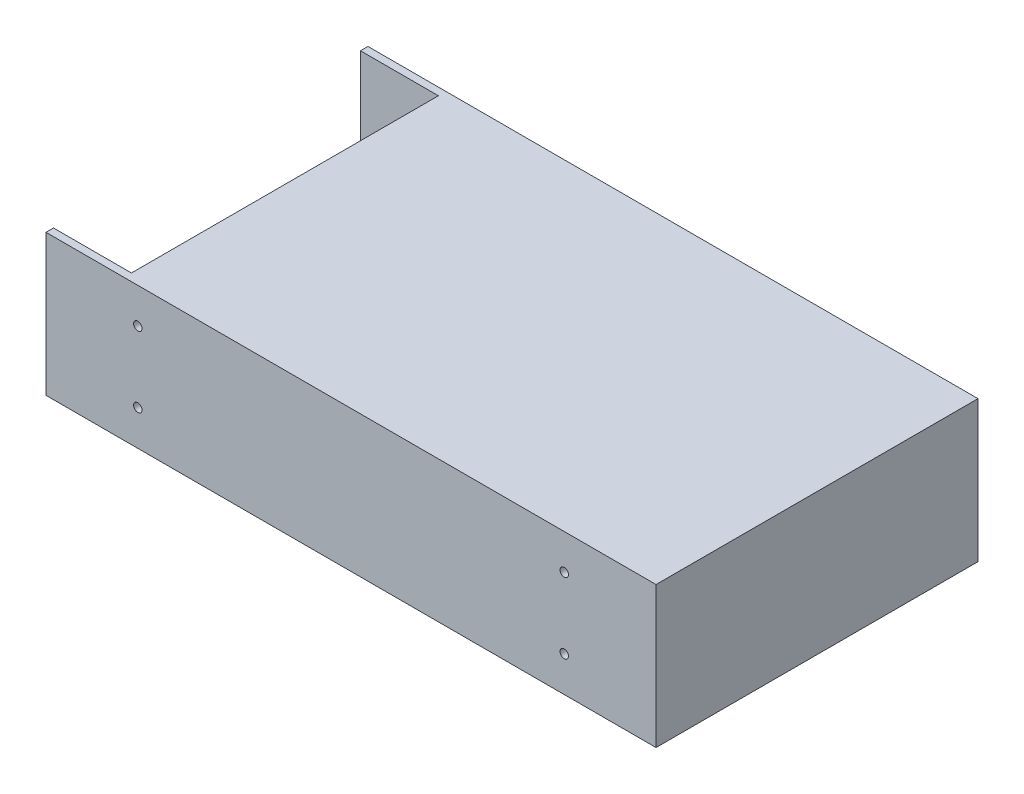
SolidWorks part; units mm, degrees
ref_plane "前视基准面" through (0, 0, 0) normal (0, 0, 1) x (1, 0, 0)
ref_plane "上视基准面" through (0, 0, 0) normal (0, 1, 0) x (1, 0, 0)
ref_plane "右视基准面" through (0, 0, 0) normal (1, 0, 0) x (0, 0, -1)
sketch "草图1" plane through (0, 0, 0) normal (0, 1, 0) x (1, 0, 0)
  line L0 (0, 0) -> (48559.8577, 0) construction
  line L1 (0, 0) -> (0, 48559.8577) construction
  line L3 (-108, 57) -> (108, 57)
  line L4 (-108, 57) -> (-108, -57)
  line L5 (-108, -57) -> (108, -57)
  line L6 (108, 57) -> (108, -57)
  dimension "D1" = 216
  dimension "D2" = 114
extrude "凸台-拉伸1" add sketch "草图1" along normal blind 50
sketch "草图2" plane through (0, 50, 0) normal (0, 1, 0) x (1, 0, 0)
  line L0 (-108, 57) -> (-108, -57) construction
  line L1 (-108, 54.3417) -> (-80.4049, 54.3417)
  line L2 (-108, 54.3417) -> (-108, -54.3417)
  line L3 (-108, -54.3417) -> (-80.4049, -54.3417)
  line L4 (-80.4049, 54.3417) -> (-80.4049, -54.3417)
extrude "切除-拉伸1" cut sketch "草图2" against normal blind 44
sketch "草图3" plane through (0, 6, 0) normal (0, 1, 0) x (1, 0, 0)
  line L1 (-102.2979, 47.8259) -> (-86.9207, 47.8259)
  line L2 (-102.2979, 47.8259) -> (-102.2979, -47.5653)
  line L3 (-102.2979, -47.5653) -> (-86.9207, -47.5653)
  line L4 (-86.9207, 47.8259) -> (-86.9207, -47.5653)
extrude "凸台-拉伸2" add sketch "草图3" along normal blind 10
sketch "草图4" plane through (0, 0, 57) normal (0, 0, 1) x (1, 0, 0)
  line L0 (108, 50) -> (108, 0) construction
  line L1 (-108, 0) -> (108, 0) construction
  circle A0 centre (75.5, 37.5) radius 1.5
  circle A1 centre (75.5, 12.5) radius 1.5
  circle A2 centre (-75.5, 12.5) radius 1.5
  circle A3 centre (-75.5, 37.5) radius 1.5
  dimension "D1" = 25
  dimension "D2" = 151
  dimension "D3" = 3
  dimension "D5" = 12.5
  dimension "D4" = 32.5
extrude "切除-拉伸2" cut sketch "草图4" against normal through all
